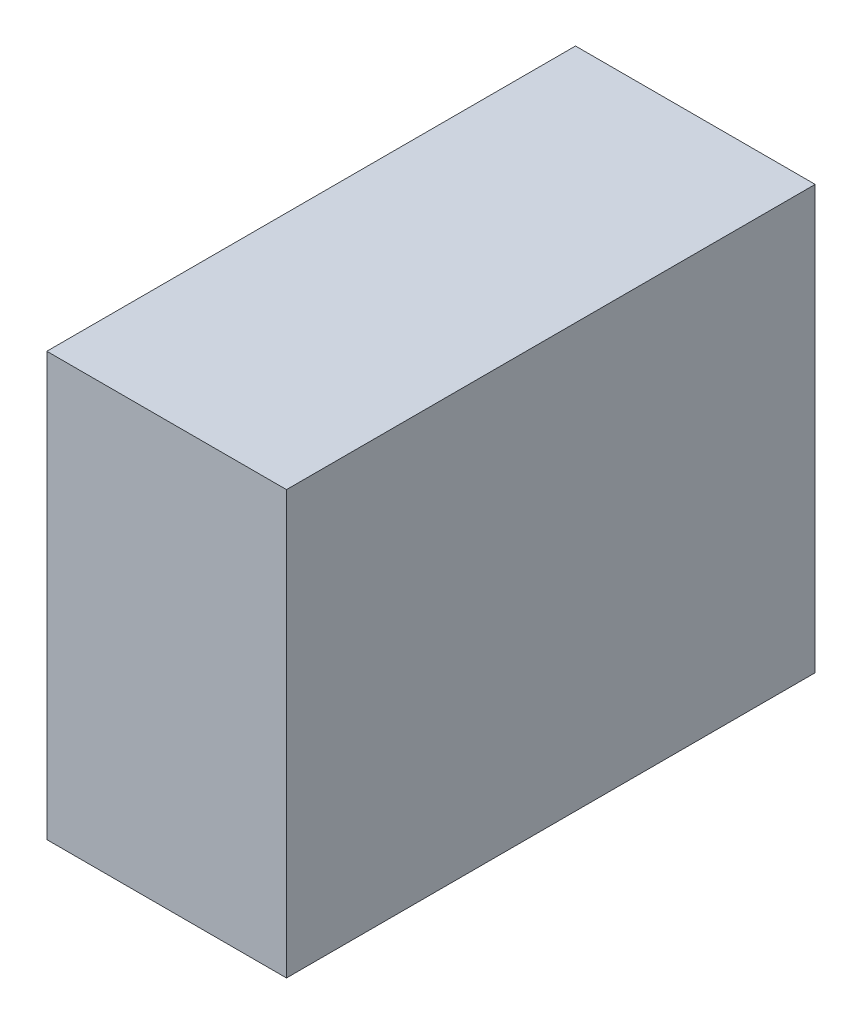
SolidWorks part; units mm, degrees
ref_plane "Alzado" through (0, 0, 0) normal (0, 0, 1) x (1, 0, 0)
ref_plane "Planta" through (0, 0, 0) normal (0, 1, 0) x (1, 0, 0)
ref_plane "Vista lateral" through (0, 0, 0) normal (1, 0, 0) x (0, 0, -1)
sketch "Croquis1" plane through (0, 0, 0) normal (0, 0, 1) x (1, 0, 0)
  line L0 (0, 0) -> (68, 120) construction
  line L1 (0, 0) -> (68, 0)
  line L2 (0, 0) -> (0, 120)
  line L3 (0, 120) -> (68, 120)
  line L4 (68, 0) -> (68, 120)
  circle A0 centre (34, 60) radius 68.9638 construction
  circle A1 centre (34, 60) radius 90 construction
  dimension "D3" = 180
  dimension "D1" = 68
  dimension "D2" = 120
extrude "Saliente-Extruir1" add sketch "Croquis1" along normal blind 150
